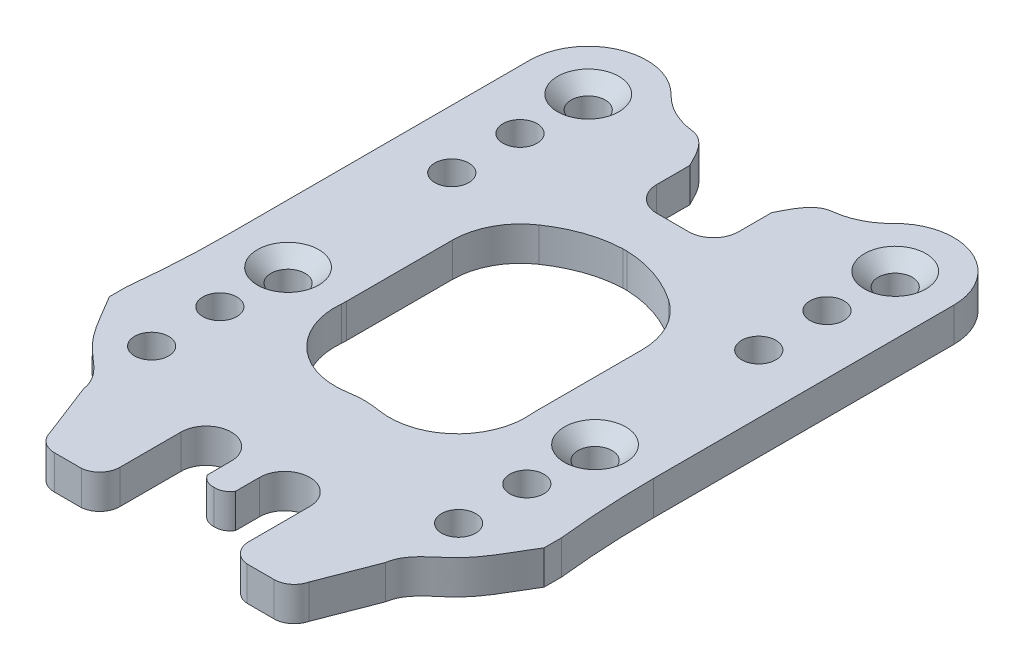
SolidWorks part; units mm, degrees
material "6063-T1"
ref_plane "Front Plane" through (0, 0, 0) normal (0, 0, 1) x (1, 0, 0)
ref_plane "Top Plane" through (0, 0, 0) normal (0, 1, 0) x (1, 0, 0)
ref_plane "Right Plane" through (0, 0, 0) normal (1, 0, 0) x (0, 0, -1)
sketch "Sketch1" plane through (0, 0, 0) normal (0, 1, 0) x (1, 0, 0)
  line L0 (144.6667, 430) -> (723.3333, 430) construction
  line L12 (59.7862, 74.2991) -> (14.7862, 74.2991) construction
  line L13 (59.7862, 74.2991) -> (59.7862, 30.2991) construction
  line L14 (59.7862, 30.2991) -> (14.7862, 30.2991) construction
  line L15 (14.7862, 30.2991) -> (14.7862, 74.2991) construction
  line L16 (37.2862, 74.2991) -> (37.2862, 30.2991) construction
  line L29 (69.1544, 13.4709) -> (69.1544, 16.004)
  line L30 (68.3732, 53.5825) -> (68.3732, 48.1333)
  line L32 (43.2843, 67.8376) -> (43.2843, 72.6916)
  line L34 (59.3827, -0.0495) -> (56.2565, -8.1388)
  line L35 (49.4018, -10.3578) -> (53.399, -10.3578)
  line L36 (46.7311, 1.5458) -> (46.7311, -7.4085)
  line L37 (39.6289, 64.1822) -> (34.9435, 64.1822)
  line L38 (39.3589, 1.5458) -> (39.3589, -1.9562)
  line L39 (35.2136, 1.5458) -> (35.2136, -1.9562)
  line L40 (37.5904, 57.1984) -> (36.9821, 57.1984)
  line L41 (27.8413, 1.5458) -> (27.8413, -7.4085)
  line L42 (25.1706, -10.3578) -> (21.1734, -10.3578)
  line L43 (15.1897, -0.0495) -> (18.3159, -8.1388)
  line L45 (31.2881, 67.8376) -> (31.2881, 72.6916)
  line L47 (6.1993, 53.5825) -> (6.1993, 48.1333)
  line L48 (5.418, 13.4709) -> (5.418, 16.004)
  line L50 (59.7862, 54.2991) -> (14.7862, 54.2991) construction
  line L51 (59.7862, 54.2991) -> (59.7862, 10.2991) construction
  line L52 (59.7862, 10.2991) -> (14.7862, 10.2991) construction
  line L53 (14.7862, 10.2991) -> (14.7862, 54.2991) construction
  line L54 (6.1993, 74.2991) -> (6.1993, 53.5825)
  line L55 (68.3732, 74.2991) -> (68.3732, 53.5825)
  line L56 (68.3732, 48.1333) -> (68.3732, 30.2991)
  line L57 (6.1993, 48.1333) -> (6.1993, 30.2991)
  line L58 (23.3732, 30.2991) -> (23.3732, 45.7796)
  line L59 (51.1993, 30.2991) -> (51.1993, 45.7796)
  arc A25 (46.7311, 1.5458) -> (39.3589, 1.5458) centre (43.045, 1.5458) ccw
  arc A26 (39.6289, 64.1822) -> (43.2843, 67.8376) centre (39.6289, 67.8376) ccw
  arc A29 (53.399, -10.3578) -> (56.2565, -8.1388) centre (53.399, -7.4085) ccw
  arc A30 (46.7311, -7.4085) -> (49.4018, -10.3578) centre (49.695, -7.4085) ccw
  arc A31 (37.2862, -3.0521) -> (39.3589, -1.9562) centre (37.4376, -0.8304) ccw
  arc A32 (37.2862, -3.0521) -> (35.2136, -1.9562) centre (37.1348, -0.8304) cw
  arc A33 (27.8413, -7.4085) -> (25.1706, -10.3578) centre (24.8774, -7.4085) cw
  arc A34 (21.1734, -10.3578) -> (18.3159, -8.1388) centre (21.1734, -7.4085) cw
  arc A37 (34.9435, 64.1822) -> (31.2881, 67.8376) centre (34.9435, 67.8376) cw
  arc A38 (27.8413, 1.5458) -> (35.2136, 1.5458) centre (31.5274, 1.5458) cw
  arc A42 (20.9658, 80.2613) -> (6.1993, 74.2991) centre (14.7862, 74.2991) ccw
  arc A44 (68.3732, 74.2991) -> (53.6066, 80.2613) centre (59.7862, 74.2991) ccw
  arc A45 (23.3398, 29.5423) -> (23.3732, 30.2991) centre (14.7862, 30.2991) ccw
  arc A48 (47.6046, 77.2763) -> (53.6066, 80.2613) centre (46.4102, 87.2048) ccw
  arc A51 (51.1993, 30.2991) -> (51.2327, 29.5423) centre (59.7862, 30.2991) ccw
  arc A52 (6.1993, 30.2991) -> (5.418, 16.004) centre (-124.9717, 30.2991) cw
  arc A53 (68.3732, 30.2991) -> (69.1544, 16.004) centre (199.5441, 30.2991) ccw
  arc A54 (20.9658, 80.2613) -> (26.9678, 77.2763) centre (28.1622, 87.2048) ccw
  arc A55 (51.1993, 45.7796) -> (46.7826, 54.0758) centre (41.1993, 45.7796) ccw
  arc A56 (23.3732, 45.7796) -> (27.7898, 54.0758) centre (33.3732, 45.7796) cw
  arc A57 (39.7529, 18.7771) -> (51.2327, 29.5423) centre (41.2716, 28.6611) ccw
  arc A58 (34.8195, 18.7771) -> (23.3398, 29.5423) centre (33.3008, 28.6611) cw
  spline S8 degree 3 poles (39.7529, 18.7771) (39.3414, 18.8403) (38.5185, 18.9495) (37.6966, 19.0036) (37.2862, 19.0116) knots 0.850974 0.850974 0.850974 0.850974 0.895462 0.939951 0.939951 0.939951 0.939951
  spline S9 degree 3 poles (46.7826, 54.0758) (44.0729, 55.8994) (41.0197, 57.0803) (37.5904, 57.1984) knots 0.681705 0.681705 0.681705 0.681705 1 1 1 1
  spline S10 degree 3 poles (43.2843, 72.6916) (43.9879, 74.0723) (45.1379, 76.6953) (47.258, 77.2347) (47.6046, 77.2763) knots 0 0 0 0 0.393067 0.466811 0.466811 0.466811 0.466811
  spline S11 degree 3 poles (69.1544, 13.4709) (67.526, 10.9039) (65.1245, 5.6235) (59.8069, 2.6957) (59.3827, -0.0495) knots 0 0 0 0 0.546917 1 1 1 1
  spline S12 degree 3 poles (27.7898, 54.0758) (30.4995, 55.8994) (33.5527, 57.0803) (36.9821, 57.1984) knots 0.681705 0.681705 0.681705 0.681705 1 1 1 1
  spline S13 degree 3 poles (34.8195, 18.7771) (35.231, 18.8403) (36.054, 18.9495) (36.8758, 19.0036) (37.2862, 19.0116) knots 0.850974 0.850974 0.850974 0.850974 0.895462 0.939951 0.939951 0.939951 0.939951
  spline S14 degree 3 poles (5.418, 13.4709) (7.0464, 10.9039) (9.4479, 5.6235) (14.7655, 2.6957) (15.1897, -0.0495) knots 0 0 0 0 0.546917 1 1 1 1
  spline S15 degree 3 poles (31.2881, 72.6916) (30.5845, 74.0723) (29.4346, 76.6953) (27.3144, 77.2347) (26.9678, 77.2763) knots 0 0 0 0 0.393067 0.466811 0.466811 0.466811 0.466811
  point P39 (14.7862, 10.2991)
  point P40 (59.7862, 10.2991)
  point P41 (59.7862, 54.2991)
  point P42 (14.7862, 54.2991)
  point P43 (14.7862, 74.2991)
  point P44 (59.7862, 74.2991)
  point P45 (59.7862, 30.2991)
  point P46 (14.7862, 30.2991)
  point P49 (14.7862, 64.2991)
  point P50 (59.7862, 64.2991)
  point P51 (14.7862, 20.2991)
  point P52 (59.7862, 20.2991)
  point P67 (37.2862, 77.1984)
  point P68 (37.2862, 84.1822)
  point P165 (37.2862, 57.1984)
  point P166 (37.2862, 64.1822)
  dimension "D1" = 2
  dimension "D2" = 10
extrude "Boss-Extrude1" add sketch "Sketch1" along normal blind 5
hole_wizard "M6 Clearance Hole1" positions "Sketch4" profile "Sketch5" hole size "M6" standard "ANSI Metric" end condition through all
sketch "Sketch4" plane through (0, 5, 0) normal (0, 1, 0) x (1, 0, 0)
  point P0 (14.7862, 74.2991)
  point P3 (59.7862, 74.2991)
  point P6 (14.7862, 30.2991)
  point P9 (59.7862, 30.2991)
sketch "Sketch5" plane through (14.7862, 5, -74.2991) normal (1, 0, 0) x (0, 0, 1)
  line L0 (0, 0) -> (0, 5)
  line L1 (0, 5) -> (2.5, 5)
  line L2 (2.5, 5) -> (2.5, 2)
  line L3 (2.5, 2) -> (4.5, 0)
  line L5 (4.5, 0) -> (0, 0)
  line L6 (-2.5, 2) -> (-4.5, 0) construction
  line L11 (0, -6.35) -> (0, 107.95) construction
  dimension "Thru Hole Dia." = 5
  dimension "Thru Hole Depth" = 5
  dimension "Near C'Sink Dia." = 9
  dimension "Near C'Sink Angle" = 90
hole_wizard "M6x1.0 Tapped Hole1" positions "Sketch6" profile "Sketch7" tap size "M6x1.0" standard "ANSI Metric" end condition through all
sketch "Sketch6" plane through (0, 5, 0) normal (0, 1, 0) x (1, 0, 0)
  point P0 (14.7862, 54.2991)
  point P3 (59.7862, 54.2991)
  point P6 (14.7862, 10.2991)
  point P9 (59.7862, 10.2991)
  point P13 (14.7862, 64.2991)
  point P16 (59.7862, 64.2991)
  point P19 (59.7862, 20.2991)
  point P22 (14.7862, 20.2991)
sketch "Sketch7" plane through (14.7862, 5, -54.2991) normal (1, 0, 0) x (0, 0, 1)
  line L0 (0, 0) -> (0, 5)
  line L1 (0, 5) -> (2.5, 5)
  line L2 (2.5, 5) -> (2.5, 0)
  line L5 (2.5, 0) -> (0, 0)
  line L11 (0, -6.35) -> (0, 107.95) construction
  dimension "Thru Tap Drill Dia." = 5
  dimension "Thru Tap Drill Depth" = 5
cosmetic thread "Hole Thread1" parameters "D2"=6
cosmetic thread "Hole Thread2" parameters "D2"=6
cosmetic thread "Hole Thread3" parameters "D2"=6
cosmetic thread "Hole Thread4" parameters "D2"=6
cosmetic thread "Hole Thread5" parameters "D2"=6
cosmetic thread "Hole Thread6" parameters "D2"=6
cosmetic thread "Hole Thread7" parameters "D2"=6
cosmetic thread "Hole Thread8" parameters "D2"=6
